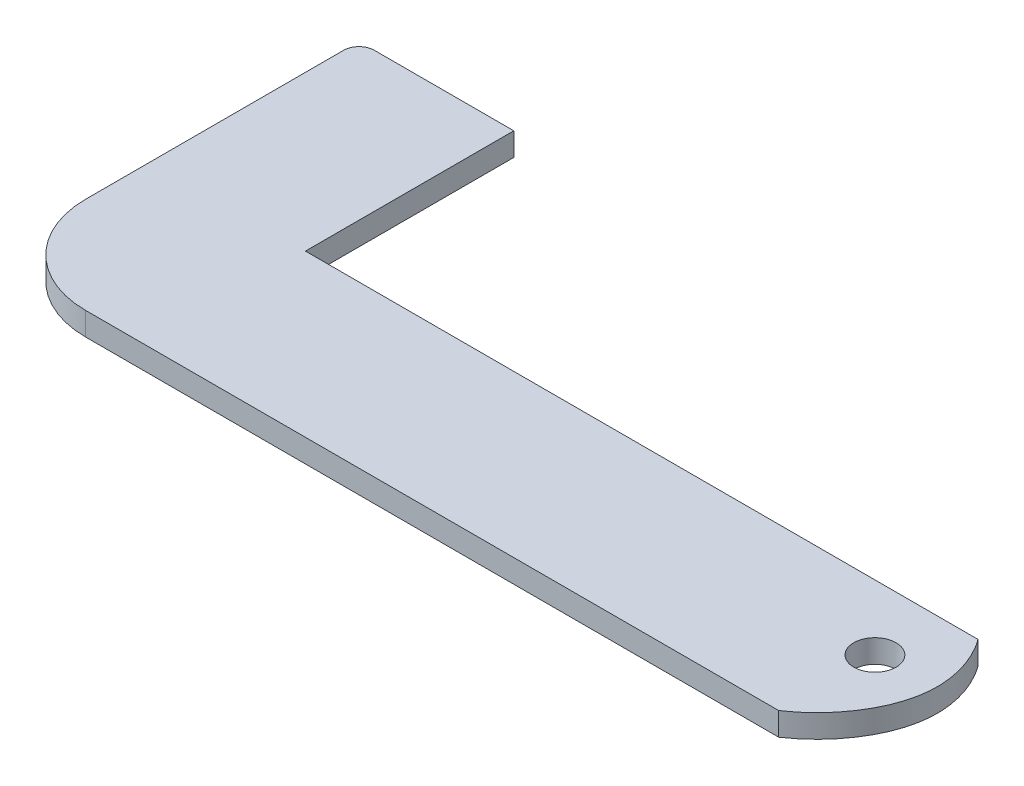
SolidWorks part; units mm, degrees
ref_plane "Front Plane" through (0, 0, 0) normal (0, 0, 1) x (1, 0, 0)
ref_plane "Top Plane" through (0, 0, 0) normal (0, 1, 0) x (1, 0, 0)
ref_plane "Right Plane" through (0, 0, 0) normal (1, 0, 0) x (0, 0, -1)
sketch "Sketch1" plane through (0, 0, 0) normal (0, 1, 0) x (1, 0, 0)
  line L3 (-45, -12.5) -> (45, -12.5)
  line L5 (0, 0) -> (45, -12.5) construction
  line L6 (-45, -12.5) -> (45, 12.5) construction
  line L7 (-37.3955, 35.5) -> (-55.5, 35.5)
  line L8 (-57.5, 33.5) -> (-57.5, 0)
  line L9 (-37.3955, 35.5) -> (-37.3955, 8.4421)
  line L10 (-37.3955, 8.4421) -> (49.9411, 8.4421)
  arc A0 (-57.5, 0) -> (-45, -12.5) centre (-45, 0) ccw
  circle A2 centre (45, 0) radius 2.75
  arc A4 (-55.5, 35.5) -> (-57.5, 33.5) centre (-55.5, 33.5) ccw
  spline S0 degree 3 poles (49.9411, 8.4421) (50.2709, 7.9938) (51.9178, 5.4471) (54.0556, -2.6849) (49.0283, -9.8228) (45, -12.5) knots 0.210172 0.210172 0.210172 0.210172 0.264235 0.503985 1 1 1 1
  point P0 (0, 0)
  point P15 (-33.1522, 35.5)
  dimension "D1" = 5.5
extrude "Boss-Extrude6" add sketch "Sketch1" along normal blind 3
